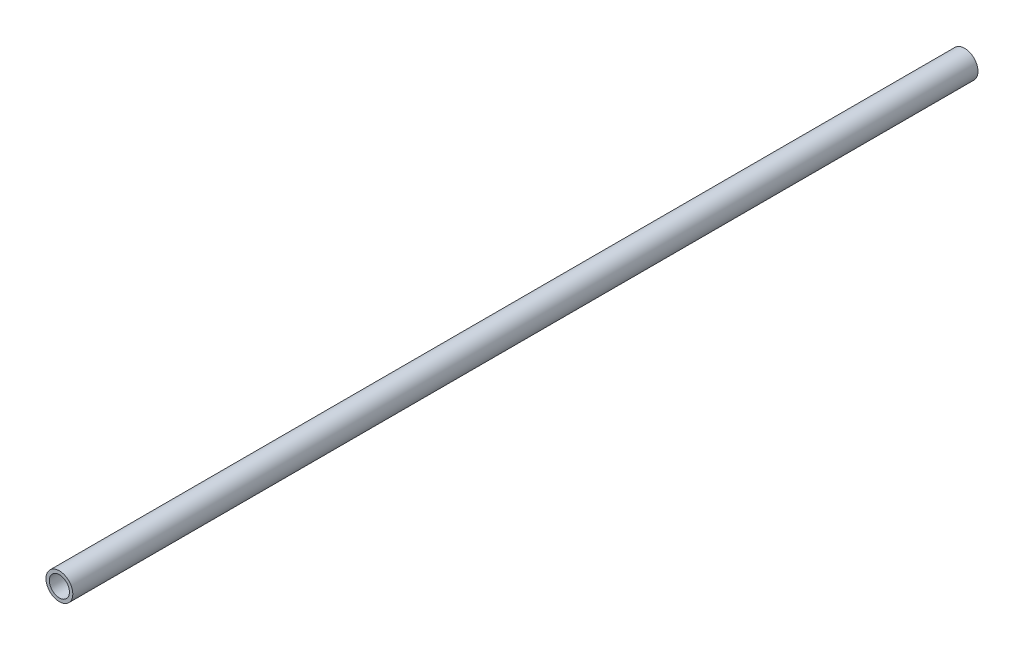
SolidWorks part; units mm, degrees
material "1023 Carbon Steel Sheet (SS)"
ref_plane "Front Plane" through (0, 0, 0) normal (0, 0, 1) x (1, 0, 0)
ref_plane "Top Plane" through (0, 0, 0) normal (0, 1, 0) x (1, 0, 0)
ref_plane "Right Plane" through (0, 0, 0) normal (1, 0, 0) x (0, 0, -1)
sketch "Sketch1" plane through (0, 0, 0) normal (0, 0, 1) x (1, 0, 0)
  circle A0 centre (0, 0) radius 8
  circle A2 centre (0, 0) radius 6
  dimension "D1" = 16
  dimension "D2" = 2
extrude "Boss-Extrude1" add sketch "Sketch1" along normal mid plane 540
